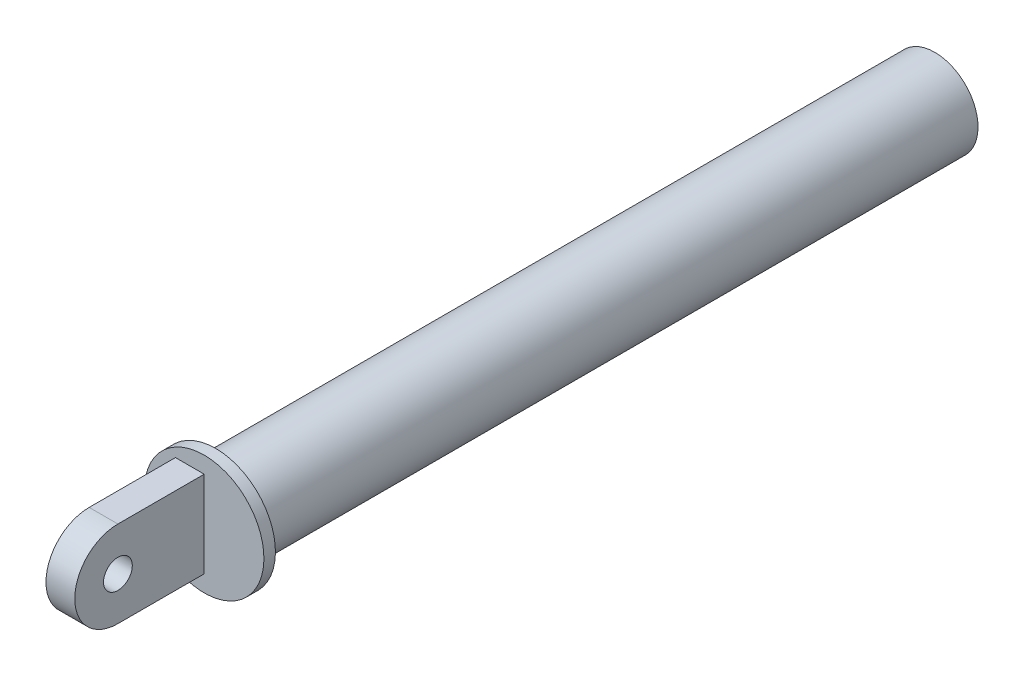
SolidWorks part; units mm, degrees
ref_plane "Front Plane" through (0, 0, 0) normal (0, 0, 1) x (1, 0, 0)
ref_plane "Top Plane" through (0, 0, 0) normal (0, 1, 0) x (1, 0, 0)
ref_plane "Right Plane" through (0, 0, 0) normal (1, 0, 0) x (0, 0, -1)
sketch "Sketch1" plane through (0, 0, 0) normal (1, 0, 0) x (0, 0, -1)
  line L1 (0, 15) -> (30, 15)
  line L3 (0, -15) -> (30, -15)
  line L4 (30, 15) -> (30, -15)
  circle A0 centre (0, 0) radius 5
  arc A1 (0, 15) -> (0, -15) centre (0, 0) ccw
  dimension "D1" = 10
  dimension "D2" = 30
  dimension "D3" = 30
extrude "Boss-Extrude1" add sketch "Sketch1" along normal mid plane 10
sketch "Sketch3" plane through (5, 0, 0) normal (1, 0, 0) x (0, 0, -1)
  line L0 (30, 15) -> (30, 20.7538)
  line L1 (30, 20.7538) -> (33.9995, 20.7538)
  line L2 (33.9995, 20.7538) -> (33.9995, 15)
  line L3 (33.9995, 15) -> (283.9995, 15)
  line L4 (283.9995, 15) -> (283.9995, 0)
  line L5 (283.9995, 0) -> (30, 0)
  line L6 (30, -15) -> (30, 15) construction
  line L7 (30, 0) -> (30, 15)
  dimension "D1" = 250
revolve "Revolve1" add sketch "Sketch3" angle 360 about L5
